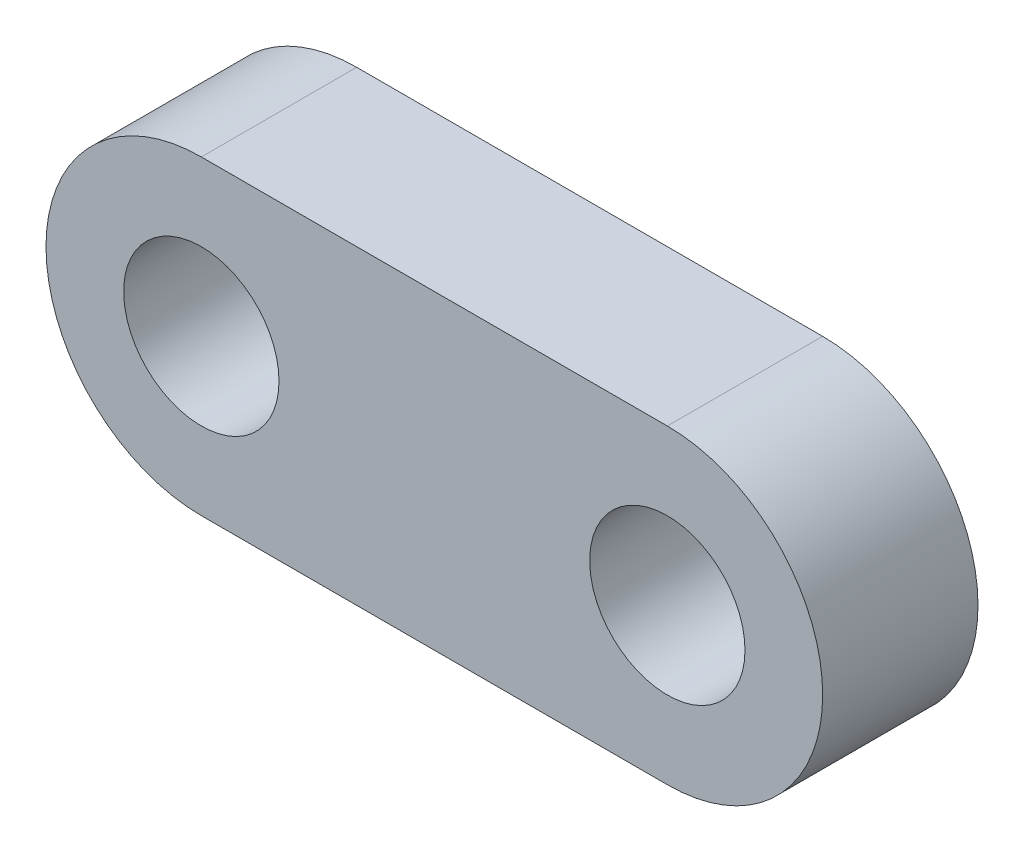
SolidWorks part; units mm, degrees
ref_plane "Front Plane" through (0, 0, 0) normal (0, 0, 1) x (1, 0, 0)
ref_plane "Top Plane" through (0, 0, 0) normal (0, 1, 0) x (1, 0, 0)
ref_plane "Right Plane" through (0, 0, 0) normal (1, 0, 0) x (0, 0, -1)
sketch "Sketch1" plane through (0, 0, 0) normal (0, 0, 1) x (1, 0, 0)
  line L0 (0, 0) -> (19.05, 0) construction
  line L1 (55, 0) -> (-55, 0) construction
  line L2 (0, 6.35) -> (19.05, 6.35)
  line L3 (0, -6.35) -> (19.05, -6.35)
  arc A0 (0, 6.35) -> (0, -6.35) centre (0, 0) ccw
  arc A1 (19.05, -6.35) -> (19.05, 6.35) centre (19.05, 0) ccw
  circle A2 centre (19.05, 0) radius 3.175
  circle A3 centre (0, 0) radius 3.175
  point P5 (9.525, 0)
  dimension "D2" = 6.35
  dimension "D3" = 6.35
  dimension "D1" = 19.05
extrude "Boss-Extrude1" add sketch "Sketch1" along normal blind 6.35
